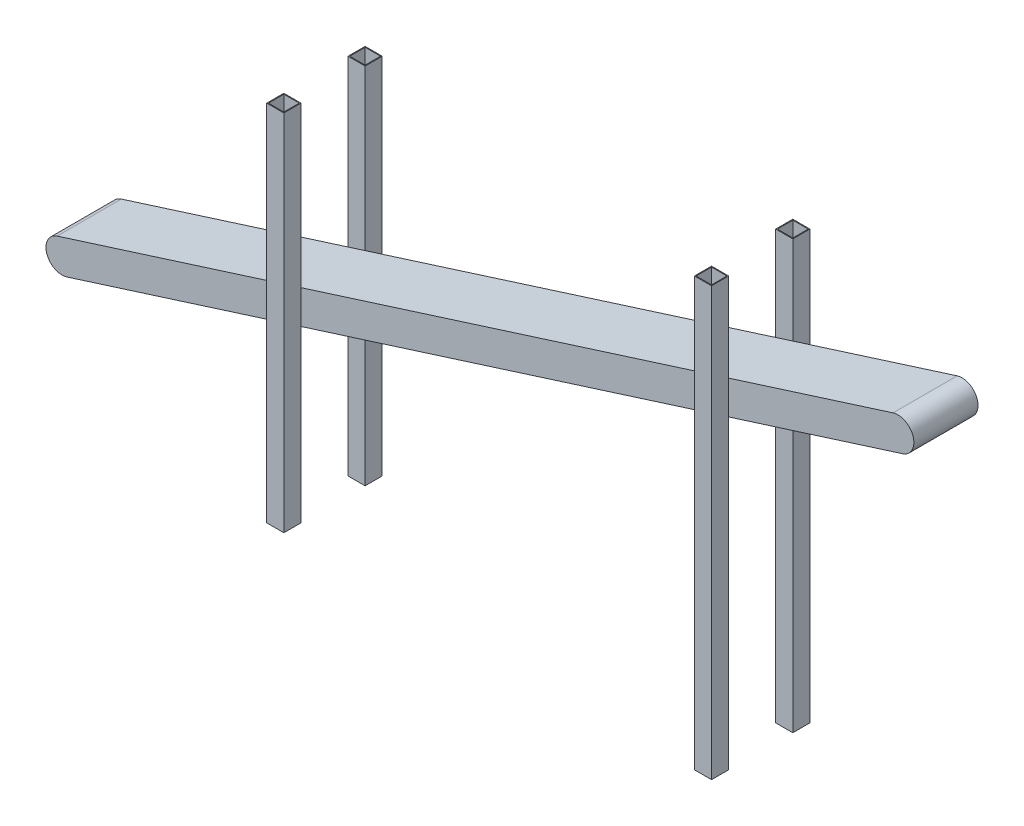
SolidWorks part; units mm, degrees
ref_plane "Front" through (0, 0, 0) normal (0, 0, 1) x (1, 0, 0)
ref_plane "Top" through (0, 0, 0) normal (0, 1, 0) x (1, 0, 0)
ref_plane "Right" through (0, 0, 0) normal (1, 0, 0) x (0, 0, -1)
sketch "Sketch1" plane through (0, 0, 0) normal (0, 0, 1) x (1, 0, 0)
  line L0 (-11.3263, 295.7486) -> (1942.9324, 914.9197)
  line L1 (1942.9324, 914.9197) -> (1965.585, 843.4224) construction
  line L2 (1965.585, 843.4224) -> (11.3263, 224.2514)
  line L3 (11.3263, 224.2514) -> (-11.3263, 295.7486) construction
  line L4 (0, 0) -> (2569.4683, 0) construction
  line L5 (515, 730.3358) -> (515, 0) construction
  line L6 (1515, 1480) -> (1515, 0) construction
  line L7 (1954.2587, 879.1711) -> (0, 260) construction
  line L8 (0, 260) -> (2099.3209, 260) construction
  line L9 (0, 0) -> (0, 351.8546) construction
  arc A0 (1942.9324, 914.9197) -> (1965.585, 843.4224) centre (1954.2587, 879.1711) cw
  arc A1 (-11.3263, 295.7486) -> (11.3263, 224.2514) centre (0, 260) ccw
  point P12 (1515, 740)
  point P13 (515, 423.1683)
  dimension "D2" = 2050
  dimension "D1" = 75
  dimension "D3" = 1000
  dimension "D4" = 740
  dimension "D5" = 260
  dimension "D6" = 515
extrude "Boss-Extrude1" add sketch "Sketch1" along normal blind 150
sketch "Sketch3" plane through (0, 0, 0) normal (0, 1, 0) x (1, 0, 0)
  line L1 (518.6737, 0) -> (558.6737, 0)
  line L2 (518.6737, 0) -> (518.6737, 40)
  line L3 (518.6737, 40) -> (558.6737, 40)
  line L4 (558.6737, 0) -> (558.6737, 40)
  line L5 (518.6737, 0) -> (558.6737, 40) construction
  line L6 (518.6737, 40) -> (558.6737, 0) construction
  line L7 (1942.9324, 0) -> (-11.3263, 0) construction
  line L8 (-130.9101, -75) -> (497.1292, -75) construction
  line L9 (1942.9324, -150) -> (-11.3263, -150) construction
  line L10 (518.6737, -190) -> (558.6737, -150) construction
  line L11 (518.6737, -150) -> (558.6737, -190) construction
  line L12 (558.6737, -150) -> (558.6737, -190)
  line L13 (518.6737, -190) -> (558.6737, -190)
  line L14 (518.6737, -150) -> (518.6737, -190)
  line L15 (518.6737, -150) -> (558.6737, -150)
  line L16 (-11.3263, -150) -> (-11.3263, 0) construction
  line L17 (520.6737, 38) -> (556.6737, 38)
  line L18 (556.6737, 2) -> (556.6737, 38)
  line L19 (520.6737, 2) -> (556.6737, 2)
  line L20 (520.6737, 2) -> (520.6737, 38)
  line L21 (520.6737, -188) -> (556.6737, -188)
  line L22 (556.6737, -152) -> (556.6737, -188)
  line L23 (520.6737, -152) -> (556.6737, -152)
  line L24 (520.6737, -152) -> (520.6737, -188)
  point P0 (538.6737, 20)
  point P15 (538.6737, -170)
  dimension "D1" = 40
  dimension "D2" = 550
  dimension "D3" = 2
  dimension "D4" = 2
extrude "Boss-Extrude2" add sketch "Sketch3" along normal blind 850
sketch "Sketch4" plane through (0, 0, 0) normal (0, 1, 0) x (1, 0, 0)
  line L0 (1942.9324, 0) -> (558.6737, 0) construction
  line L1 (1518.6737, 0) -> (1558.6737, 0)
  line L2 (1518.6737, 0) -> (1518.6737, 40)
  line L3 (1518.6737, 40) -> (1558.6737, 40)
  line L4 (1558.6737, 0) -> (1558.6737, 40)
  line L5 (1320.5212, -75) -> (1722.7872, -75) construction
  line L6 (1942.9324, -150) -> (558.6737, -150) construction
  line L7 (1558.6737, -150) -> (1558.6737, -190)
  line L8 (1518.6737, -190) -> (1558.6737, -190)
  line L9 (1518.6737, -150) -> (1518.6737, -190)
  line L10 (1518.6737, -150) -> (1558.6737, -150)
  line L11 (1520.6737, 38) -> (1556.6737, 38)
  line L12 (1556.6737, 2) -> (1556.6737, 38)
  line L13 (1520.6737, 2) -> (1556.6737, 2)
  line L14 (1520.6737, 2) -> (1520.6737, 38)
  line L15 (1520.6737, -152) -> (1556.6737, -152)
  line L16 (1556.6737, -152) -> (1556.6737, -188)
  line L17 (1520.6737, -188) -> (1556.6737, -188)
  line L18 (1520.6737, -152) -> (1520.6737, -188)
  dimension "D1" = 40
  dimension "D2" = 1000
  dimension "D3" = 2
extrude "Boss-Extrude3" add sketch "Sketch4" along normal blind 1000
